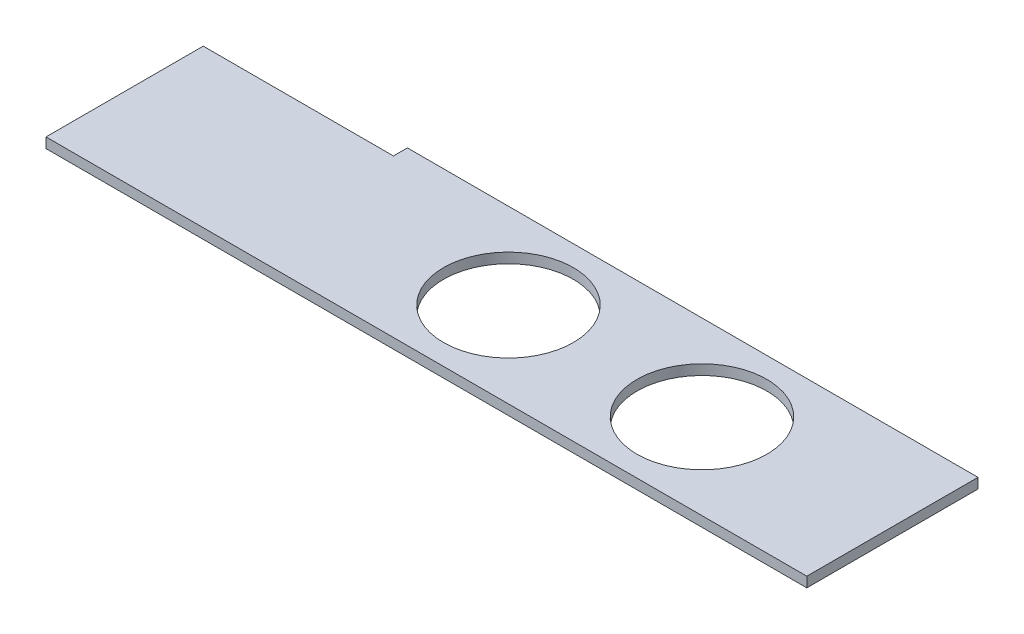
SolidWorks part; units mm, degrees
ref_plane "Front Plane" through (0, 0, 0) normal (0, 0, 1) x (1, 0, 0)
ref_plane "Top Plane" through (0, 0, 0) normal (0, 1, 0) x (1, 0, 0)
ref_plane "Right Plane" through (0, 0, 0) normal (1, 0, 0) x (0, 0, -1)
sketch "Sketch2" plane through (0, 0, 0) normal (0, 1, 0) x (1, 0, 0)
  line L0 (0, 0) -> (600, 0)
  line L1 (600, 0) -> (600, 135)
  line L3 (600, 0) -> (0, 0)
  line L4 (600, 0) -> (600, 135)
  line L5 (600, 135) -> (0, 135)
  line L6 (0, 0) -> (0, 135)
  dimension "D1" = 600
  dimension "D2" = 135
extrude "Boss-Extrude1" add sketch "Sketch2" along normal blind 8 contours L6 L0 L1 L5
sketch "Sketch3" plane through (0, 8, 0) normal (0, 1, 0) x (1, 0, 0)
  line L0 (600, 0) -> (600, 135) construction
  line L1 (0, 135) -> (150, 135)
  line L2 (0, 135) -> (0, 124)
  line L3 (0, 124) -> (150, 124)
  line L4 (150, 135) -> (150, 124)
  line L5 (600, 67.5) -> (0, 67.5) construction
  line L6 (0, 0) -> (0, 135) construction
  line L7 (147, 67.5) -> (297.2, 67.5) construction
  line L8 (0, 0) -> (600, 0) construction
  line L9 (147, 124) -> (147, 0) construction
  circle A0 centre (449.8, 67.5) radius 51.2
  circle A1 centre (297.2, 67.5) radius 51.2
  point P21 (0, 0)
  dimension "D3" = 102.4
  dimension "D10" = 102.4
  dimension "D1" = 11
  dimension "D2" = 150
  dimension "D4" = 150.2
  dimension "D5" = 67.5
  dimension "D6" = 67.5
  dimension "D7" = 3
  dimension "D8" = 0
  dimension "D9" = 150.2
extrude "Cut-Extrude1" cut sketch "Sketch3" against normal blind 8
